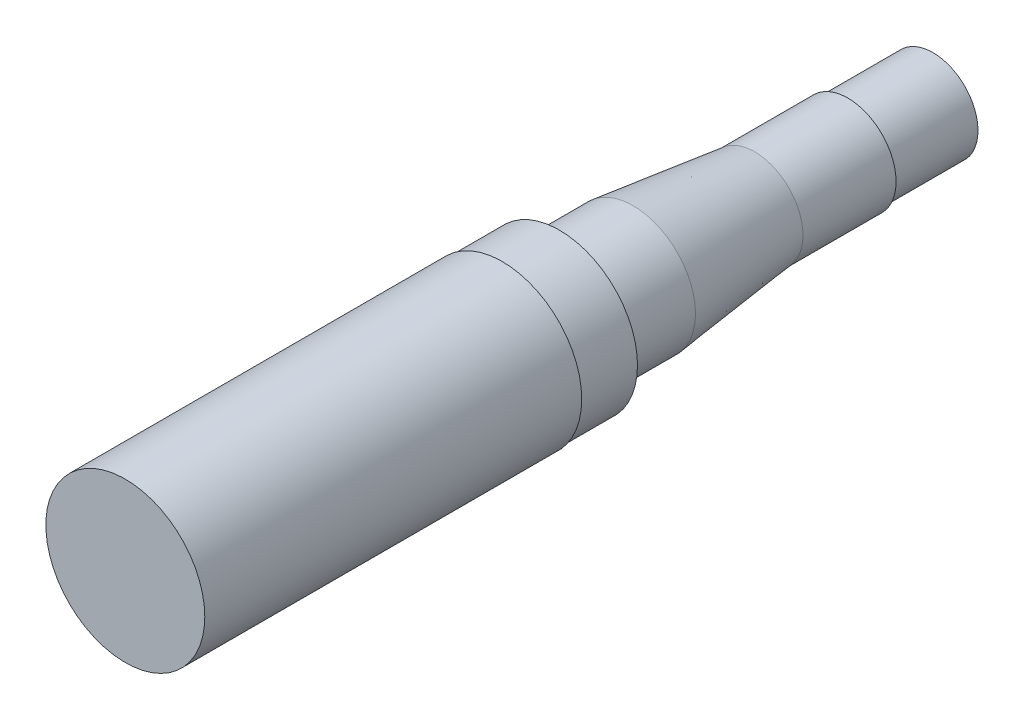
SolidWorks part; units mm, degrees
material "ASTM A36 Steel"
ref_plane "Front Plane" through (0, 0, 0) normal (0, 0, 1) x (1, 0, 0)
ref_plane "Top Plane" through (0, 0, 0) normal (0, 1, 0) x (1, 0, 0)
ref_plane "Right Plane" through (0, 0, 0) normal (1, 0, 0) x (0, 0, -1)
sketch "Sketch1" plane through (0, 0, 0) normal (1, 0, 0) x (0, 0, -1)
  line L0 (0, 0) -> (0, 22.225)
  line L1 (0, 55) -> (0, -55) construction
  line L2 (0, 22.225) -> (105.41, 22.225)
  line L3 (105.41, 22.225) -> (105.41, 21.8186)
  line L4 (105.41, 21.8186) -> (121.412, 21.8186)
  line L5 (121.412, 21.8186) -> (121.412, 19.3675)
  line L6 (123.317, 17.4625) -> (141.986, 17.4625)
  line L7 (141.986, 17.4625) -> (176.022, 13.4874)
  line L8 (176.022, 13.4874) -> (202.057, 13.4874)
  line L9 (202.057, 13.4874) -> (202.057, 13.2334)
  line L10 (202.692, 12.5984) -> (204.597, 12.5984)
  line L11 (204.597, 12.5984) -> (225.8568, 12.5984)
  line L12 (225.8568, 12.5984) -> (225.8568, 0)
  line L13 (0, 0) -> (225.8568, 0) construction
  line L14 (0, 0) -> (225.8568, 0)
  arc A0 (121.412, 19.3675) -> (123.317, 17.4625) centre (123.317, 19.3675) ccw
  arc A1 (202.057, 13.2334) -> (202.692, 12.5984) centre (202.692, 13.2334) ccw
  dimension "D2" = 1.905
  dimension "D3" = 0.635
  dimension "D1" = 44.45
  dimension "D4" = 105.41
  dimension "D5" = 16.002
  dimension "D6" = 20.574
  dimension "D7" = 104.4448
  dimension "D8" = 54.61
  dimension "D9" = 80.645
  dimension "D10" = 2.54
  dimension "D11" = 43.6372
  dimension "D12" = 34.925
  dimension "D13" = 26.9748
  dimension "D14" = 25.1968
revolve "Revolve1" add sketch "Sketch1" angle 360 mid plane about L13
